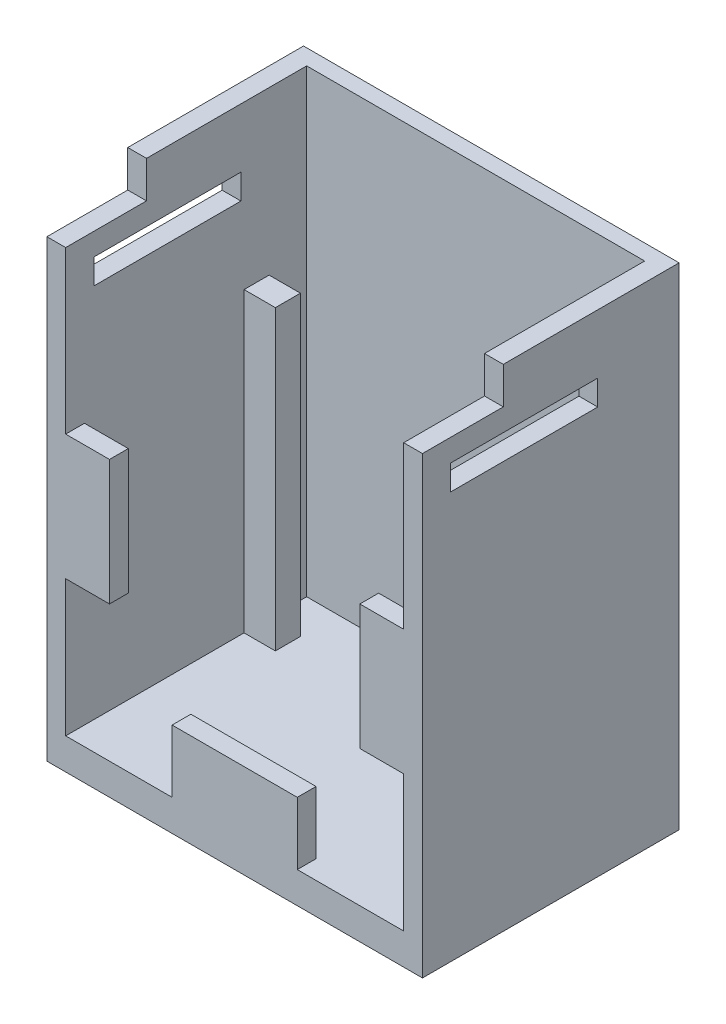
SolidWorks part; units mm, degrees
material "ABS"
ref_plane "Front Plane" through (0, 0, 0) normal (0, 0, 1) x (1, 0, 0)
ref_plane "Top Plane" through (0, 0, 0) normal (0, 1, 0) x (1, 0, 0)
ref_plane "Right Plane" through (0, 0, 0) normal (1, 0, 0) x (0, 0, -1)
sketch "Sketch1" plane through (0, 0, 0) normal (0, 0, 1) x (1, 0, 0)
  line L1 (15.24, -25.4) -> (-15.24, -25.4)
  line L2 (15.24, -25.4) -> (15.24, 15.24)
  line L3 (15.24, 15.24) -> (-15.24, 15.24)
  line L4 (-15.24, -25.4) -> (-15.24, 15.24)
  point P0 (0, 0)
  dimension "D1" = 30.48
  dimension "D2" = 40.64
extrude "Initial Block" add sketch "Sketch1" along normal blind 19.05 and the other way blind 1.778
sketch "Sketch2" plane through (0, 15.24, 0) normal (0, 1, 0) x (1, 0, 0)
  line L0 (15.24, 1.778) -> (-15.24, 1.778) construction
  line L1 (-13.716, 0.508) -> (13.716, 0.508)
  line L2 (-13.716, 0.508) -> (-13.716, -19.05)
  line L3 (-13.716, -19.05) -> (13.716, -19.05)
  line L4 (13.716, 0.508) -> (13.716, -19.05)
  line L5 (0, 1.778) -> (0, -14.7779) construction
  line L6 (15.24, -19.05) -> (-15.24, -19.05) construction
  point P9 (0, 1.778)
  point P11 (0, 0.508)
  point P12 (0, 0.508)
  dimension "D1" = 27.432
  dimension "D2" = 1.27
  dimension "D3" = 0
extrude "Initial Cut" cut sketch "Sketch2" against normal blind 38.1
ref_plane "Plane1" through (0, 0, 19.05) normal (0, 0, 1) x (1, 0, 0)
ref_plane "Plane2" through (0, 0, 0) normal (1, 0, 0) x (0, 0, -1)
sketch "Sketch20" plane through (0, 0, 19.05) normal (0, 0, 1) x (1, 0, 0)
  line L0 (-15.24, 9.398) -> (-15.24, -22.86) construction
  line L1 (-15.24, -22.86) -> (15.24, -22.86) construction
  line L2 (15.24, -22.86) -> (15.24, 9.398) construction
  line L3 (-15.24, -6.731) -> (15.24, -6.731) construction
  line L4 (15.24, 9.398) -> (-15.24, 9.398) construction
  line L5 (-15.24, -11.811) -> (-10.16, -11.811)
  line L6 (-15.24, -11.811) -> (-15.24, -1.651)
  line L7 (-15.24, -1.651) -> (-10.16, -1.651)
  line L8 (-10.16, -11.811) -> (-10.16, -1.651)
  line L9 (0, 9.398) -> (0, -22.86) construction
  line L10 (15.24, -11.811) -> (15.24, -1.651)
  line L11 (-5.08, -17.78) -> (5.08, -17.78)
  line L12 (-5.08, -17.78) -> (-5.08, -22.86)
  line L13 (-5.08, -22.86) -> (5.08, -22.86)
  line L14 (5.08, -17.78) -> (5.08, -22.86)
  line L15 (15.24, -11.811) -> (10.16, -11.811)
  line L16 (10.16, -11.811) -> (10.16, -1.651)
  line L17 (15.24, -1.651) -> (10.16, -1.651)
  line L19 (-13.716, -22.86) -> (13.716, -22.86) construction
  line L23 (-15.24, 15.24) -> (-15.24, -25.4) construction
  line L24 (15.24, -25.4) -> (15.24, 15.24) construction
  dimension "D1" = 10.16
  dimension "D2" = 5.08
  dimension "D3" = 10.16
  dimension "D4" = 5.08
  dimension "D5" = 5.08
  dimension "D6" = 10.16
extrude "Boss-Extrude1" add sketch "Sketch20" against normal blind 1.524
sketch "Sketch21" plane through (-13.716, 0, 0) normal (1, 0, 0) x (0, 0, -1)
  line L0 (-19.05, -1.651) -> (-19.05, 15.24) construction
  line L1 (-4.572, 1.27) -> (-2.54, 1.27)
  line L2 (-4.572, 1.27) -> (-4.572, -22.86)
  line L3 (-4.572, -22.86) -> (-2.54, -22.86)
  line L4 (-2.54, 1.27) -> (-2.54, -22.86)
  line L5 (0.508, 15.24) -> (-19.05, 15.24) construction
  line L6 (0.508, -22.86) -> (-19.05, -22.86) construction
  dimension "D1" = 2.032
  dimension "D2" = 14.478
  dimension "D3" = 13.97
  dimension "D4" = 0
extrude "Boss-Extrude2" add sketch "Sketch21" along normal blind 2.54 contours L4 L3 L2 L1
mirror "Mirror2" about plane through (0, 0, 0) normal (1, 0, 0) of "Boss-Extrude2"
sketch "Sketch27" plane through (15.24, 0, 0) normal (1, 0, 0) x (0, 0, -1)
  line L0 (-16.764, 9.652) -> (-4.826, 9.652)
  line L1 (-16.764, 9.652) -> (-16.764, 7.62)
  line L2 (-16.764, 7.62) -> (-4.826, 7.62)
  line L3 (-4.826, 9.652) -> (-4.826, 7.62)
  line L5 (-19.05, -25.4) -> (-19.05, 15.24) construction
  line L7 (1.778, -25.4) -> (-19.05, -25.4) construction
  dimension "D1" = 11.938
  dimension "D2" = 2.032
  dimension "D3" = 33.02
  dimension "D4" = 2.286
extrude "Cut-Extrude6" cut sketch "Sketch27" against normal up to next (1.524 mm away)
mirror "Mirror6" about plane through (0, 0, 0) normal (1, 0, 0) of "Cut-Extrude6"
sketch "Sketch28" plane through (0, 0, 19.05) normal (0, 0, 1) x (1, 0, 0)
  line L0 (15.24, -25.4) -> (15.24, 15.24) construction
  line L1 (-15.24, 15.24) -> (15.24, 15.24)
  line L2 (-15.24, 15.24) -> (-15.24, 13.462)
  line L3 (-15.24, 13.462) -> (15.24, 13.462)
  line L4 (15.24, 15.24) -> (15.24, 13.462)
  dimension "D1" = 1.778
extrude "Cut-Extrude7" cut sketch "Sketch28" against normal through all
sketch "Sketch29" plane through (0, 0, 19.05) normal (0, 0, 1) x (1, 0, 0)
  line L0 (15.24, -25.4) -> (15.24, 13.462) construction
  line L1 (-15.24, 13.462) -> (15.24, 13.462)
  line L2 (-15.24, 13.462) -> (-15.24, 11.462)
  line L3 (-15.24, 11.462) -> (15.24, 11.462)
  line L4 (15.24, 13.462) -> (15.24, 11.462)
  dimension "D1" = 2
extrude "Cut-Extrude8" cut sketch "Sketch29" against normal blind 5.81
sketch "Sketch30" plane through (0, 13.462, 0) normal (0, 1, 0) x (1, 0, 0)
  line L0 (-15.24, -13.24) -> (-15.24, 1.778)
  line L1 (-15.24, 1.778) -> (15.24, 1.778)
  line L2 (15.24, 1.778) -> (15.24, -13.24)
  line L3 (15.24, -13.24) -> (13.716, -13.24)
  line L4 (13.716, -13.24) -> (13.716, 0.508)
  line L5 (13.716, 0.508) -> (-13.716, 0.508)
  line L6 (-13.716, 0.508) -> (-13.716, -13.24)
  line L7 (-13.716, -13.24) -> (-15.24, -13.24)
extrude "Boss-Extrude3" add sketch "Sketch30" along normal blind 0.99
sketch "Sketch31" plane through (0, 0, 13.24) normal (0, 0, 1) x (1, 0, 0)
  line L0 (15.24, 11.462) -> (15.24, 14.452) construction
  line L1 (-15.24, 14.452) -> (15.24, 14.452)
  line L2 (-15.24, 14.452) -> (-15.24, 11.462)
  line L3 (-15.24, 11.462) -> (15.24, 11.462)
  line L4 (15.24, 14.452) -> (15.24, 11.462)
  line L5 (13.716, 11.462) -> (15.24, 11.462) construction
extrude "Cut-Extrude9" cut sketch "Sketch31" against normal blind 0.75
